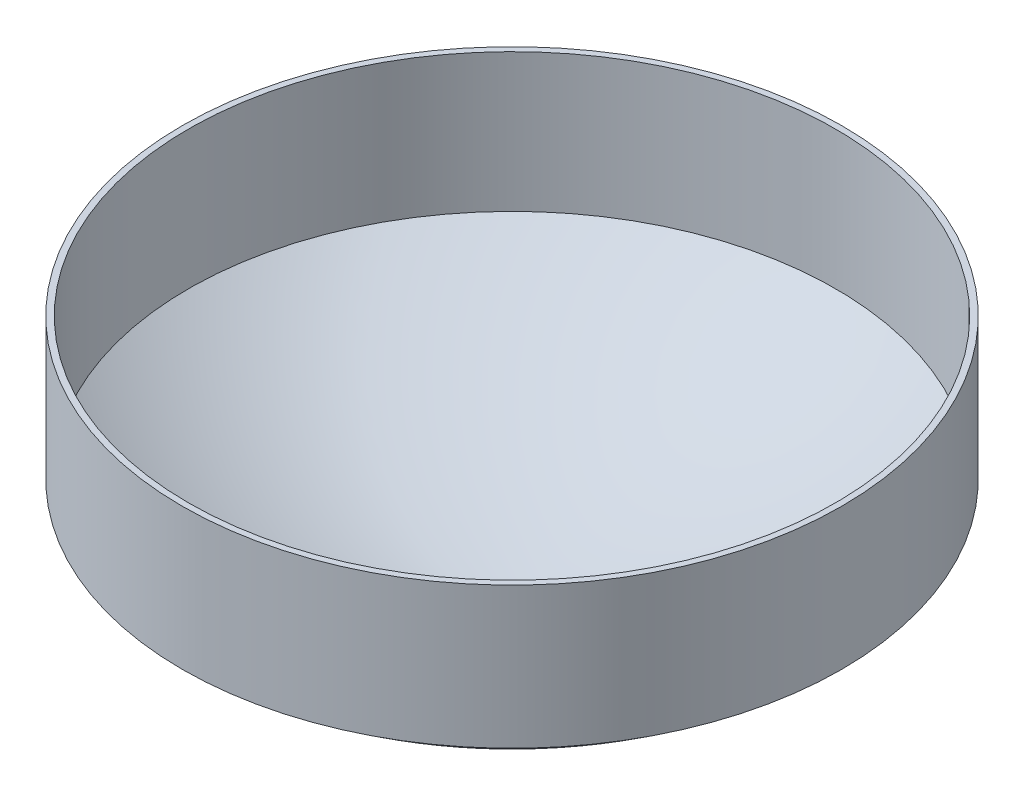
SolidWorks part; units mm, degrees
ref_plane "Front Plane" through (0, 0, 0) normal (0, 0, 1) x (1, 0, 0)
ref_plane "Top Plane" through (0, 0, 0) normal (0, 1, 0) x (1, 0, 0)
ref_plane "Right Plane" through (0, 0, 0) normal (1, 0, 0) x (0, 0, -1)
sketch "Sketch1" plane through (0, 0, 0) normal (0, 1, 0) x (1, 0, 0)
  circle A0 centre (0, 0) radius 177.8
  circle A1 centre (0, 0) radius 174.5488
  dimension "D1" = 355.6
  dimension "D2" = 3.2512
extrude "Boss-Extrude1" add sketch "Sketch1" along normal blind 76.2
ref_plane "Plane1" through (0, -67.31, 0) normal (0, 1, 0) x (1, 0, 0)
sketch "Sketch2" plane through (0, 0, 0) normal (1, 0, 0) x (0, 0, -1)
  line L0 (0, 76.2) -> (0, -67.31) construction
  line L1 (174.5488, 76.2) -> (-174.5488, 76.2) construction
  line L2 (195.58, -67.31) -> (-195.58, -67.31) construction
  line L3 (0, 80.3275) -> (0, -80.3275) construction
  line L4 (0, -67.31) -> (15.1765, -67.31) construction
  line L5 (195.58, 0) -> (-195.58, 0) construction
  line L6 (0, -69.85) -> (15.1765, -69.85) construction
  line L7 (15.1765, -67.31) -> (15.1765, -64.0335)
  line L8 (177.8, 0) -> (175.804, 2.5664)
  arc A0 (15.1765, -67.31) -> (177.8, 0) centre (-25.7892, 261.7719) ccw
  arc A1 (15.1765, -64.0335) -> (175.804, 2.5664) centre (-25.7892, 261.7719) ccw
  arc A2 (14.7749, -64.0837) -> (175.804, 2.5664) centre (-25.7892, 261.7719) ccw construction
  dimension "D1" = 15.1765
  dimension "D2" = 2.54
  dimension "D3" = 3.2512
revolve "Revolve1" add sketch "Sketch2" angle 360 about L0
